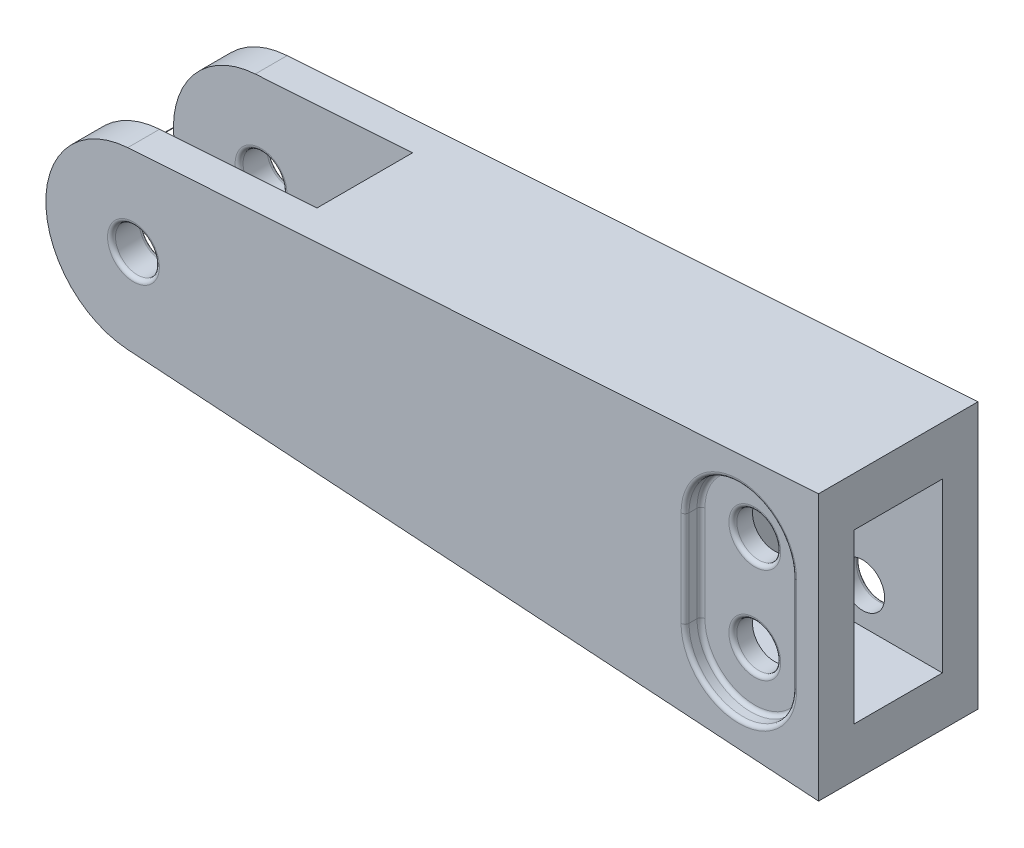
SolidWorks part; units mm, degrees
ref_plane "Front Plane" through (0, 0, 0) normal (0, 0, 1) x (1, 0, 0)
ref_plane "Top Plane" through (0, 0, 0) normal (0, 1, 0) x (1, 0, 0)
ref_plane "Right Plane" through (0, 0, 0) normal (1, 0, 0) x (0, 0, -1)
sketch "Sketch1" plane through (0, 0, 0) normal (0, 0, 1) x (1, 0, 0)
  line L1 (43.0973, 0) -> (50043.0973, 0) construction
  line L2 (0, 21.9801) -> (0, 50021.9801) construction
  line L5 (-147.5823, 10.9687) -> (-60.9236, 16.6957)
  line L6 (-60.9236, -16.6957) -> (-17.5178, -19.5642) construction
  line L7 (-60.9236, 16.6957) -> (-60.9236, -16.6957) construction
  line L8 (-60.9236, 16.6957) -> (-60.9236, -16.6957)
  line L9 (-147.5823, -10.9687) -> (-60.9236, -16.6957)
  arc A1 (-147.5823, 10.9687) -> (-147.5823, -10.9687) centre (-146.8574, 0) ccw
  point P9 (0, 0)
  dimension "D1" = 146.8574
extrude "Boss-Extrude1" add sketch "Sketch1" along normal up to surface (20 mm away)
sketch "Sketch2" plane through (-60.9236, 0, 0) normal (1, 0, 0) x (0, 0, -1)
  line L0 (-10, -20) -> (-10, 20) construction
  line L4 (-15.535, -10.535) -> (-4.465, -10.535)
  line L5 (-15.535, -10.535) -> (-15.535, 10.535)
  line L6 (-15.535, 10.535) -> (-4.465, 10.535)
  line L16 (-20, -20) -> (0, -20) construction
  line L17 (-20, 20) -> (-20, -20) construction
  line L18 (0, 20) -> (-20, 20) construction
  line L19 (0, -20) -> (0, 20) construction
  line L20 (-4.465, -10.535) -> (-4.465, 10.535)
  line L21 (-15.535, -10.535) -> (-4.465, 10.535) construction
  line L22 (-15.535, 10.535) -> (-4.465, -10.535) construction
  line L23 (0, 0) -> (-20, 0) construction
  point P2 (-10, 0)
  point P15 (-10, 0)
  dimension "D2" = 11.07
  dimension "D3" = 21.07
  dimension "D1" = 40
  dimension "D4" = 20
  dimension "D5" = 10
extrude "Cut-Extrude1" cut sketch "Sketch2" against normal blind 20
sketch "Sketch4" plane through (0, 0, 0) normal (0, 1, 0) x (1, 0, 0)
  line L0 (-60.9236, -20) -> (-147.5823, -20) construction
  line L5 (-157.85, 0) -> (-157.85, -20) construction
  line L6 (-157.85, -4) -> (-127.85, -4)
  line L7 (-157.85, -4) -> (-157.85, -16)
  line L10 (-157.85, -16) -> (-127.85, -16)
  line L15 (-127.85, -4) -> (-127.85, -16)
  line L16 (-157.85, -4) -> (-127.85, -16) construction
  line L17 (-157.85, -16) -> (-127.85, -4) construction
  line L18 (-147.5823, 0) -> (-157.8501, 0) construction
  point P4 (-142.85, -10)
  dimension "D1" = 4
  dimension "D2" = 4
  dimension "D3" = 30
extrude "Cut-Extrude2" cut sketch "Sketch4" against normal through all both and the other way through all
sketch "Sketch5" plane through (0, 0, 0) normal (0, 0, -1) x (-1, 0, 0)
  circle A0 centre (146.8574, 0) radius 2.75
  dimension "D1" = 5.5
extrude "Cut-Extrude3" cut sketch "Sketch5" against normal through all
sketch "Sketch6" plane through (0, 0, 0) normal (0, 0, -1) x (-1, 0, 0)
  line L1 (0, 0) -> (50000, 0) construction
  line L2 (60.9236, 16.6957) -> (60.9236, -16.6957) construction
  circle A0 centre (70.9236, -6) radius 2.75
  circle A1 centre (70.9236, 6) radius 2.75
  dimension "D1" = 5.5
  dimension "D2" = 10
  dimension "D3" = 6
extrude "Cut-Extrude4" cut sketch "Sketch6" against normal through all
sketch "Sketch8" plane through (0, 0, 0) normal (0, 0, -1) x (-1, 0, 0)
  line L0 (64.1736, 6) -> (64.1736, -6)
  line L2 (77.6736, 6) -> (77.6736, -6)
  circle A0 centre (70.9236, -6) radius 2.75 construction
  circle A1 centre (70.9236, 6) radius 2.75 construction
  circle A2 centre (70.9236, -6) radius 2.75 construction
  circle A3 centre (70.9236, 6) radius 2.75 construction
  arc A4 (64.1736, -6) -> (77.6736, -6) centre (70.9236, -6) ccw
  arc A5 (77.6736, 6) -> (64.1736, 6) centre (70.9236, 6) ccw
  circle A6 centre (70.9236, 6) radius 6.75 construction
  circle A7 centre (70.9236, -6) radius 6.75 construction
  dimension "D1" = 4
extrude "Cut-Extrude5" cut sketch "Sketch8" against normal blind 2
ref_plane "Plane1" through (0, 0, 10) normal (0, 0, -1) x (-1, 0, 0)
mirror "Mirror1" about plane through (0, 0, 10) normal (0, 0, -1) of "Cut-Extrude5"
fillet "Fillet2" radius 0.5 24 edges at (-70.9236, 12.75, 18) (-64.1736, 0, 18) (-70.9236, -12.75, 18) (-77.6736, 0, 18) (-68.1736, 6, 18) (-70.9236, 12.75, 20) (-64.1736, 0, 20) (-70.9236, -12.75, 20) (-77.6736, 0, 20) (-68.1736, -6, 18) (-149.6074, 0, 4) (-149.6074, 0, 20) (-144.1074, 0, 16) (-149.6074, 0, 0) (-73.6736, 6, 2) (-70.9236, 12.75, 0) (-64.1736, 0, 0) (-70.9236, -12.75, 0) (-77.6736, 0, 0) (-70.9236, 12.75, 2) (-77.6736, 0, 2) (-70.9236, -12.75, 2) (-64.1736, 0, 2) (-73.6736, -6, 2)
